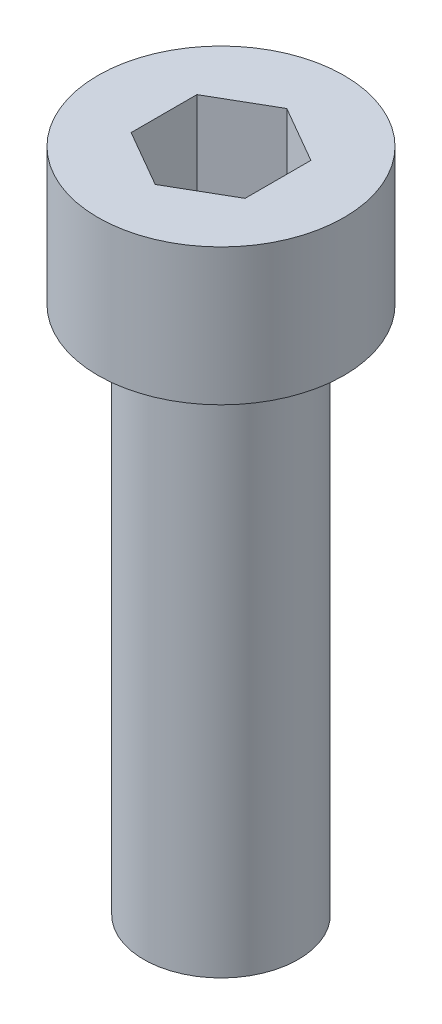
SolidWorks part; units mm, degrees
ref_plane "Front Plane" through (0, 0, 0) normal (0, 0, 1) x (1, 0, 0)
ref_plane "Top Plane" through (0, 0, 0) normal (0, 1, 0) x (1, 0, 0)
ref_plane "Right Plane" through (0, 0, 0) normal (1, 0, 0) x (0, 0, -1)
sketch "Sketch1" plane through (0, 0, 0) normal (0, 1, 0) x (1, 0, 0)
  circle A0 centre (184.7145, -125.2443) radius 2.7
  dimension "D1" = 5.4
extrude "Boss-Extrude1" add sketch "Sketch1" against normal blind 3
sketch "Sketch2" plane through (0, -3, 0) normal (0, -1, 0) x (1, 0, 0)
  circle A0 centre (184.7145, 125.2443) radius 1.6963
extrude "Boss-Extrude2" add sketch "Sketch2" along normal blind 11.6
sketch "Sketch3" plane through (0, 0, 0) normal (0, 1, 0) x (1, 0, 0)
  line L1 (184.7145, -123.8009) -> (183.4645, -124.5226)
  line L2 (183.4645, -124.5226) -> (183.4645, -125.966)
  line L3 (183.4645, -125.966) -> (184.7145, -126.6877)
  line L4 (184.7145, -126.6877) -> (185.9645, -125.966)
  line L5 (185.9645, -125.966) -> (185.9645, -124.5226)
  line L6 (185.9645, -124.5226) -> (184.7145, -123.8009)
  circle A0 centre (184.7145, -125.2443) radius 1.25 construction
  dimension "D1" = 2.5
extrude "Cut-Extrude1" cut sketch "Sketch3" against normal blind 2
